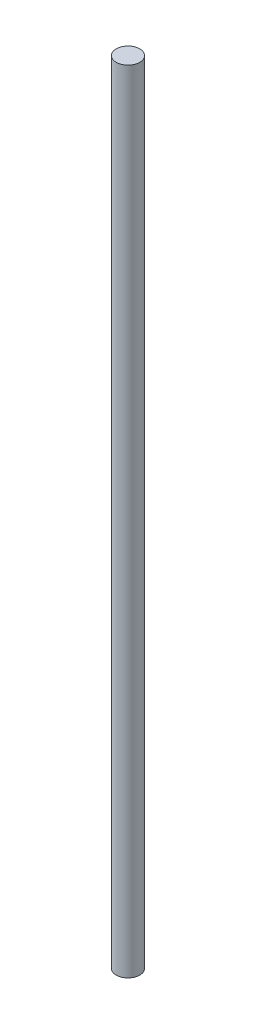
SolidWorks part; units mm, degrees
ref_plane "Front Plane" through (0, 0, 0) normal (0, 0, 1) x (1, 0, 0)
ref_plane "Top Plane" through (0, 0, 0) normal (0, 1, 0) x (1, 0, 0)
ref_plane "Right Plane" through (0, 0, 0) normal (1, 0, 0) x (0, 0, -1)
sketch "Sketch1" plane through (0, 0, 0) normal (0, 1, 0) x (1, 0, 0)
  circle A0 centre (0, 0) radius 4
  dimension "D1" = 8
extrude "Boss-Extrude1" add sketch "Sketch1" along normal blind 270
